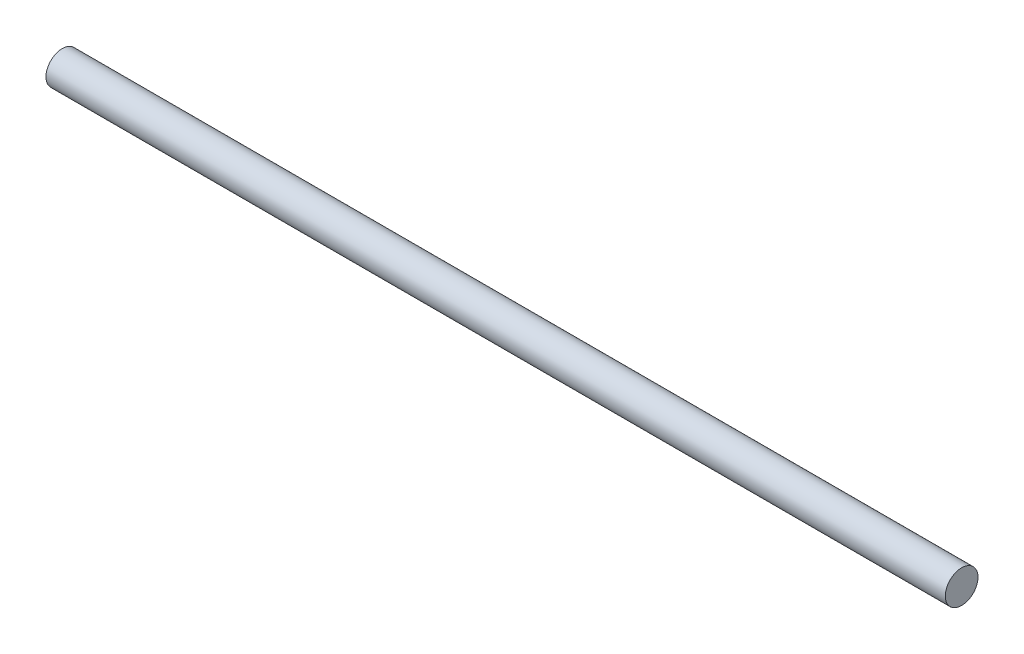
SolidWorks part; units mm, degrees
material "Легированная сталь"
ref_plane "Спереди" through (0, 0, 0) normal (0, 0, 1) x (1, 0, 0)
ref_plane "Сверху" through (0, 0, 0) normal (0, 1, 0) x (1, 0, 0)
ref_plane "Справа" through (0, 0, 0) normal (1, 0, 0) x (0, 0, -1)
other "Configuration Table"
sketch "Эскиз1" plane through (0, 0, 0) normal (1, 0, 0) x (0, 0, -1)
  circle A0 centre (0, 0) radius 4
  dimension "D1" = 8
extrude "Бобышка-Вытянуть1" add sketch "Эскиз1" along normal blind 220
ref_plane "Плоскость1" through (0, 4, 0) normal (0, 1, 0) x (1, 0, 0)
sketch "Эскиз3" plane through (0, 4, 0) normal (0, 1, 0) x (1, 0, 0)
  line L0 (10, 0) -> (110, 0)
  line L1 (36.4303, -7.5023) -> (36.4303, 10.0362) construction
  line L2 (136.4303, -7.15) -> (136.4303, 7.15) construction
  dimension "D1" = 200
  dimension "D2" = 100
  dimension "D3" = 100
